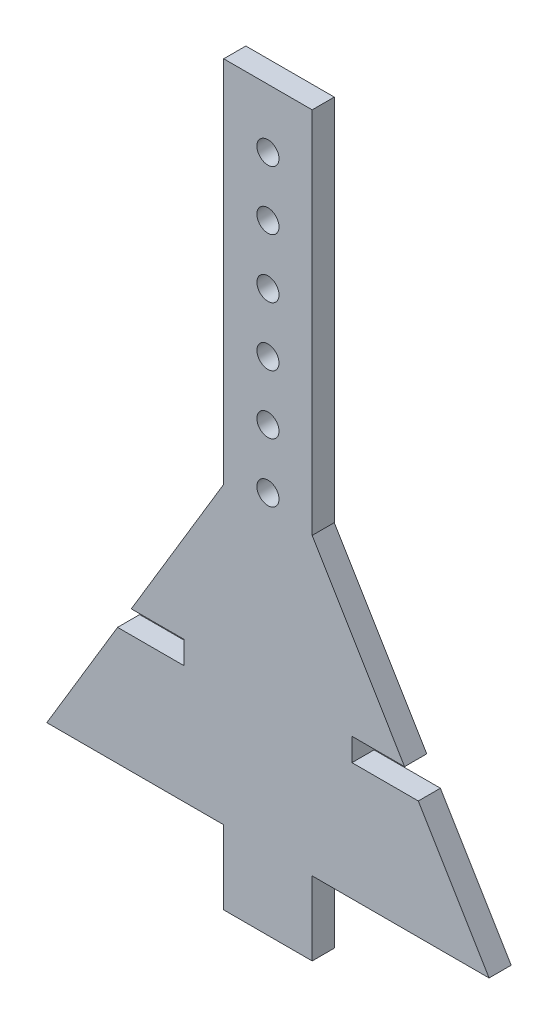
SolidWorks part; units mm, degrees
ref_plane "Plan de face" through (0, 0, 0) normal (0, 0, 1) x (1, 0, 0)
ref_plane "Plan de dessus" through (0, 0, 0) normal (0, 1, 0) x (1, 0, 0)
ref_plane "Plan de droite" through (0, 0, 0) normal (1, 0, 0) x (0, 0, -1)
sketch "Esquisse1" plane through (0, 0, 0) normal (0, 0, 1) x (1, 0, 0)
  line L0 (-30, 0) -> (-150, -200)
  line L1 (30, -250) -> (-30, -250)
  line L2 (30, -250) -> (30, -200)
  line L3 (30, 250) -> (-30, 250)
  line L4 (-30, -250) -> (-30, -200)
  line L5 (30, -250) -> (-30, 250) construction
  line L6 (30, 250) -> (-30, -250) construction
  line L7 (-150, -200) -> (-30, -200)
  line L8 (-30, 0) -> (-30, 250)
  line L9 (0, -233.2533) -> (0, 115.5769) construction
  line L10 (150, -200) -> (30, -200)
  line L11 (30, 0) -> (150, -200)
  line L12 (30, 0) -> (30, 250)
  circle A0 centre (0, 210) radius 7.5
  circle A1 centre (0, 170) radius 7.5
  circle A2 centre (0, 130) radius 7.5
  circle A3 centre (0, 90) radius 7.5
  circle A4 centre (0, 50) radius 7.5
  circle A5 centre (0, 10) radius 7.5
  point P0 (0, 0)
  dimension "D6" = 15
  dimension "D7" = 40
  dimension "D1" = 60
  dimension "D2" = 120
  dimension "D3" = 500
  dimension "D4" = 200
  dimension "D5" = 50
  dimension "D8" = 6
extrude "Boss.-Extru.1" add sketch "Esquisse1" along normal blind 15
sketch "Esquisse2" plane through (0, 0, 15) normal (0, 0, 1) x (1, 0, 0)
  line L0 (-30, -200) -> (-30, -250) construction
  line L1 (-147.9899, -104.5) -> (-57, -104.5)
  line L2 (-147.9899, -104.5) -> (-147.9899, -120)
  line L3 (-147.9899, -120) -> (-57, -120)
  line L4 (-57, -104.5) -> (-57, -120)
  line L5 (-150, -200) -> (-30, -200) construction
  dimension "D1" = 27
  dimension "D2" = 80
  dimension "D3" = 15.5
extrude "Enlèv. mat.-Extru.1" cut sketch "Esquisse2" against normal blind 15
mirror "Symétrie1" about plane through (0, 0, 0) normal (1, 0, 0) of "Enlèv. mat.-Extru.1"
